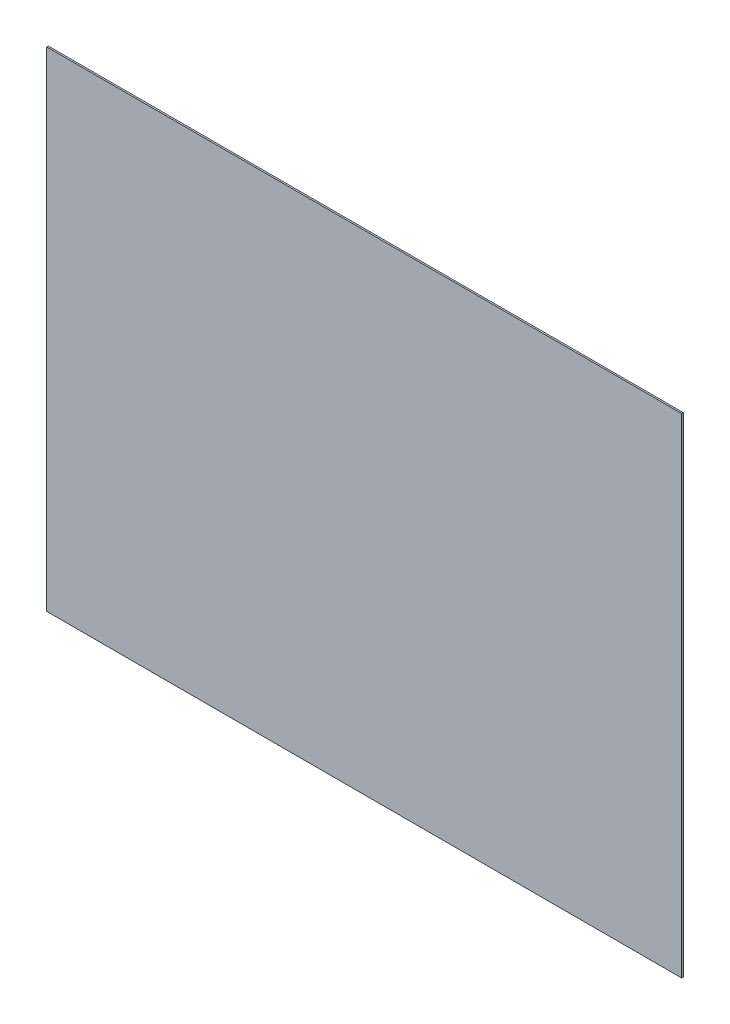
SolidWorks part; units mm, degrees
material "3.0205 (EN-AW 1200)"
ref_plane "정면" through (0, 0, 0) normal (0, 0, 1) x (1, 0, 0)
ref_plane "윗면" through (0, 0, 0) normal (0, 1, 0) x (1, 0, 0)
ref_plane "우측면" through (0, 0, 0) normal (1, 0, 0) x (0, 0, -1)
sketch "스케치1" plane through (0, 0, 0) normal (0, 0, 1) x (1, 0, 0)
  line L0 (0, 0) -> (400, 0)
  line L1 (400, 0) -> (400, 308)
  line L2 (400, 308) -> (330, 308)
  line L6 (20, 308) -> (0, 308)
  line L7 (0, 308) -> (0, 0)
  line L8 (330, 308) -> (20, 308)
  dimension "D1" = 400
  dimension "D2" = 308
extrude "보스-돌출1" add sketch "스케치1" along normal blind 1 contours L6 L7 L0 L1 L2 L8
